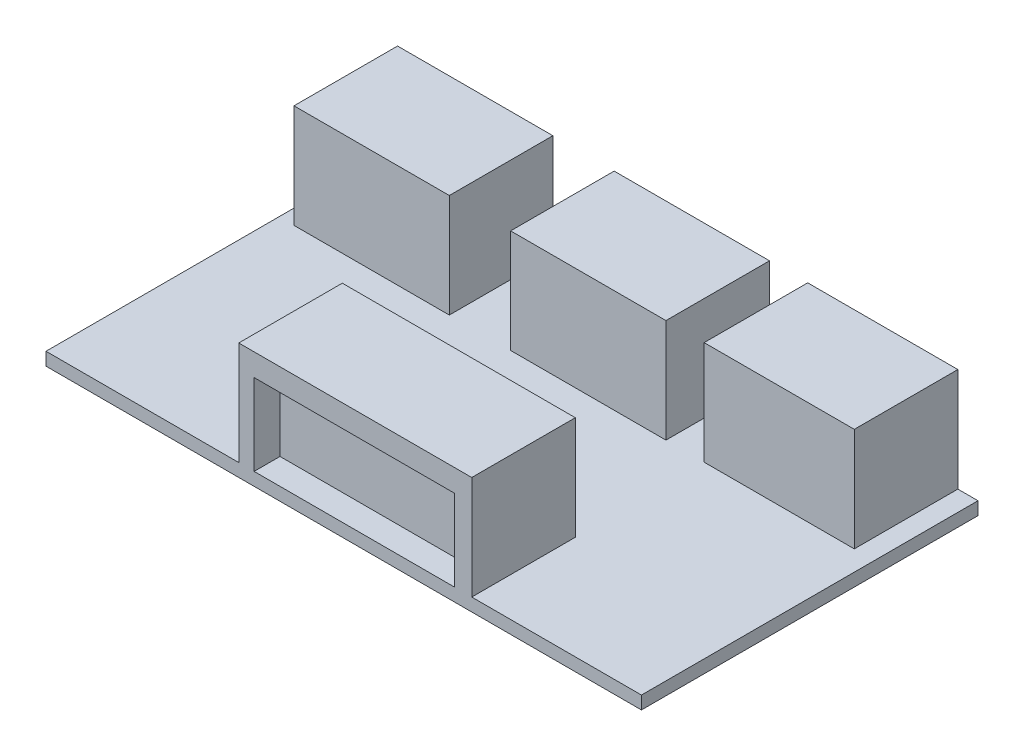
SolidWorks part; units mm, degrees
ref_plane "Front Plane" through (0, 0, 0) normal (0, 0, 1) x (1, 0, 0)
ref_plane "Top Plane" through (0, 0, 0) normal (0, 1, 0) x (1, 0, 0)
ref_plane "Right Plane" through (0, 0, 0) normal (1, 0, 0) x (0, 0, -1)
sketch "Sketch1" plane through (0, 0, 0) normal (0, 1, 0) x (1, 0, 0)
  line L1 (-9.9828, 7.5702) -> (13.0172, 7.5702)
  line L2 (-9.9828, 7.5702) -> (-9.9828, -5.4298)
  line L3 (-9.9828, -5.4298) -> (13.0172, -5.4298)
  line L4 (13.0172, 7.5702) -> (13.0172, -5.4298)
  dimension "D1" = 23
  dimension "D2" = 13
extrude "Boss-Extrude1" add sketch "Sketch1" along normal blind 0.5
sketch "Sketch2" plane through (0, 0.5, 0) normal (0, 1, 0) x (1, 0, 0)
  line L0 (13.0172, 7.5702) -> (-9.9828, 7.5702) construction
  line L1 (6.4393, 7.5702) -> (12.2393, 7.5702)
  line L2 (6.4393, 7.5702) -> (6.4393, 3.5702)
  line L3 (6.4393, 3.5702) -> (12.2393, 3.5702)
  line L4 (12.2393, 7.5702) -> (12.2393, 3.5702)
  line L5 (-9.4039, 7.5702) -> (-3.4039, 7.5702)
  line L6 (-9.4039, 7.5702) -> (-9.4039, 3.5702)
  line L7 (-9.4039, 3.5702) -> (-3.4039, 3.5702)
  line L8 (-3.4039, 7.5702) -> (-3.4039, 3.5702)
  line L9 (-1.0362, 7.5702) -> (4.9638, 7.5702)
  line L10 (-1.0362, 7.5702) -> (-1.0362, 3.5702)
  line L11 (-1.0362, 3.5702) -> (4.9638, 3.5702)
  line L12 (4.9638, 7.5702) -> (4.9638, 3.5702)
  line L13 (-9.9828, -5.4298) -> (13.0172, -5.4298) construction
  line L14 (-2.5375, -5.4298) -> (6.4625, -5.4298)
  line L15 (-2.5375, -5.4298) -> (-2.5375, -1.4298)
  line L16 (-2.5375, -1.4298) -> (6.4625, -1.4298)
  line L17 (6.4625, -5.4298) -> (6.4625, -1.4298)
  dimension "D1" = 6
  dimension "D2" = 6
  dimension "D3" = 5.8
  dimension "D4" = 4
  dimension "D5" = 9
  dimension "D6" = 4
extrude "Boss-Extrude2" add sketch "Sketch2" along normal blind 4
sketch "Sketch3" plane through (0, 0, -7.5702) normal (0, 0, -1) x (-1, 0, 0)
  line L0 (1.0362, 0.5) -> (3.4039, 0.5) construction
  line L1 (-11.7058, 3.6669) -> (-7.0817, 3.6669)
  line L2 (-11.7058, 3.6669) -> (-11.7058, 0.5)
  line L3 (-11.7058, 0.5) -> (-7.0817, 0.5)
  line L4 (-7.0817, 3.6669) -> (-7.0817, 0.5)
  line L5 (-4.2799, 3.5133) -> (0.4386, 3.5133)
  line L6 (-4.2799, 3.5133) -> (-4.2799, 0.5)
  line L7 (-4.2799, 0.5) -> (0.4386, 0.5)
  line L8 (0.4386, 3.5133) -> (0.4386, 0.5)
  line L9 (4.1471, 3.5133) -> (8.7275, 3.5133)
  line L10 (4.1471, 3.5133) -> (4.1471, 0.5)
  line L11 (4.1471, 0.5) -> (8.7275, 0.5)
  line L12 (8.7275, 3.5133) -> (8.7275, 0.5)
extrude "Cut-Extrude1" cut sketch "Sketch3" against normal blind 1
sketch "Sketch4" plane through (0, 0, 5.4298) normal (0, 0, 1) x (1, 0, 0)
  line L0 (6.4625, 0.5) -> (13.0172, 0.5) construction
  line L1 (-1.9444, 3.6403) -> (5.8044, 3.6403)
  line L2 (-1.9444, 3.6403) -> (-1.9444, 0.5)
  line L3 (-1.9444, 0.5) -> (5.8044, 0.5)
  line L4 (5.8044, 3.6403) -> (5.8044, 0.5)
extrude "Cut-Extrude2" cut sketch "Sketch4" against normal blind 1
